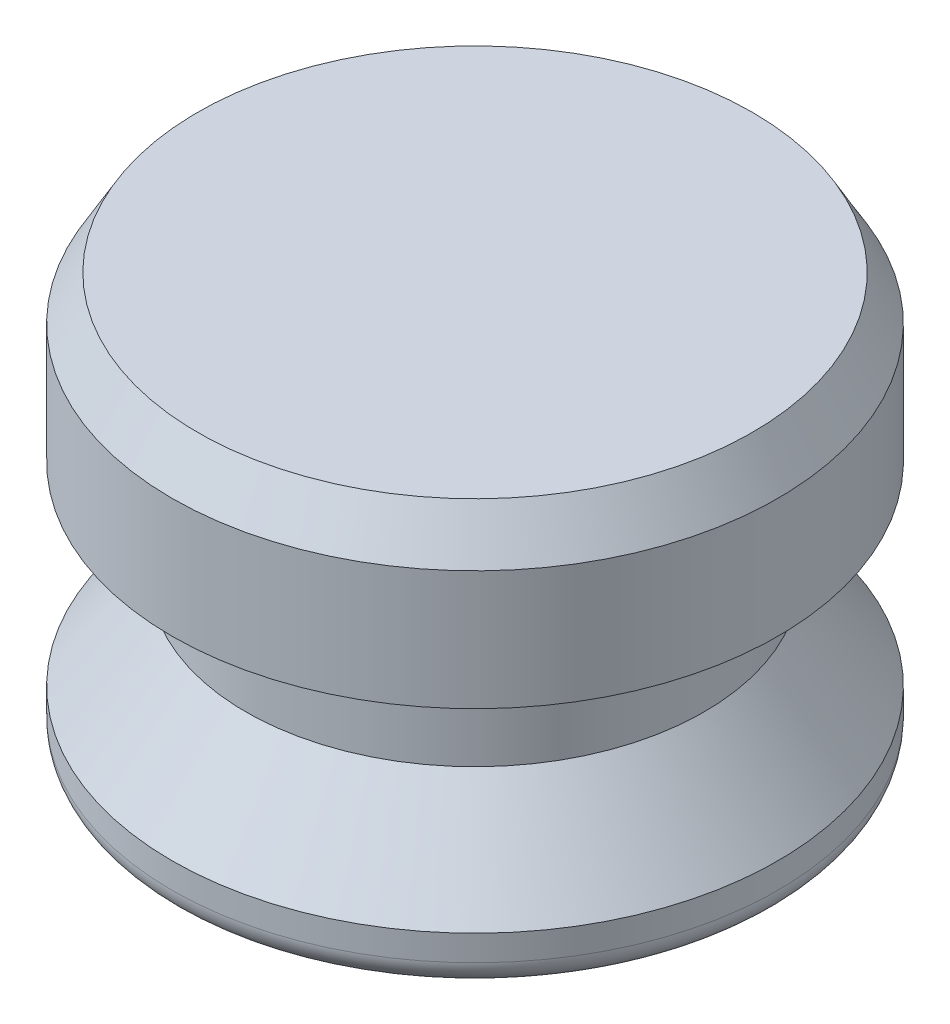
SolidWorks part; units mm, degrees
ref_plane "Front Plane" through (0, 0, 0) normal (0, 0, 1) x (1, 0, 0)
ref_plane "Top Plane" through (0, 0, 0) normal (0, 1, 0) x (1, 0, 0)
ref_plane "Right Plane" through (0, 0, 0) normal (1, 0, 0) x (0, 0, -1)
sketch "Sketch1" plane through (0, 0, 0) normal (0, 0, 1) x (1, 0, 0)
  line L0 (0, 0) -> (0, 12.7) construction
  line L1 (0, 0) -> (-9.398, 0)
  line L2 (-9.398, 0) -> (-9.398, 1.5875)
  line L4 (-7.112, 4.445) -> (-7.112, 7.62)
  line L5 (-7.112, 7.62) -> (-9.398, 7.62)
  line L6 (-9.398, 7.62) -> (-9.398, 12.7)
  line L7 (-9.398, 12.7) -> (0, 12.7)
  line L8 (-9.525, 16.6801) -> (-9.525, -9.6051) construction
  line L9 (0, 0) -> (0, 12.7)
  line L10 (-7.112, 4.445) -> (-9.398, 1.5875)
  dimension "D1" = 12.7
  dimension "D2" = 9.398
  dimension "D3" = 3.175
  dimension "D4" = 1.5875
  dimension "D5" = 9.525
  dimension "D6" = 7.112
  dimension "D7" = 7.62
revolve "Revolve1" add sketch "Sketch1" angle 360 about L9
fillet "Fillet1" radius 0.7937 1 edges at (0, 0, -9.398)
chamfer "Chamfer1" distance 0.7937 angle 60 1 edges at (0, 12.7, -9.398)
